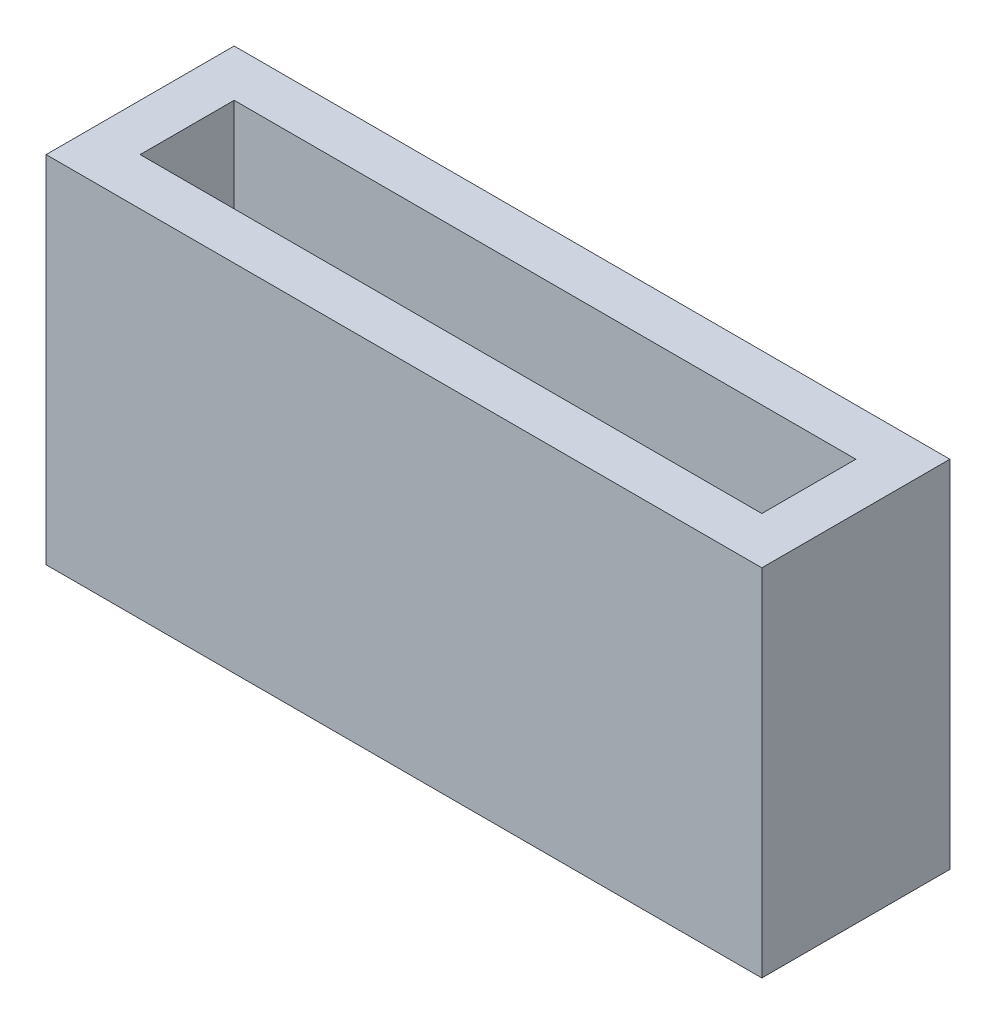
SolidWorks part; units mm, degrees
ref_plane "Front Plane" through (0, 0, 0) normal (0, 0, 1) x (1, 0, 0)
ref_plane "Top Plane" through (0, 0, 0) normal (0, 1, 0) x (1, 0, 0)
ref_plane "Right Plane" through (0, 0, 0) normal (1, 0, 0) x (0, 0, -1)
sketch "Sketch1" plane through (0, 0, 0) normal (0, 1, 0) x (1, 0, 0)
  line L1 (-55.1703, -19.7188) -> (-20.9203, -19.7188)
  line L2 (-55.1703, -19.7188) -> (-55.1703, -28.7188)
  line L3 (-55.1703, -28.7188) -> (-20.9203, -28.7188)
  line L4 (-20.9203, -19.7188) -> (-20.9203, -28.7188)
extrude "Boss-Extrude1" add sketch "Sketch1" along normal blind 17
sketch "Sketch2" plane through (0, 17, 0) normal (0, 1, 0) x (1, 0, 0)
  line L8 (-52.9203, -21.9688) -> (-52.9203, -26.4688)
  line L9 (-52.9203, -26.4688) -> (-23.1703, -26.4688)
  line L10 (-23.1703, -26.4688) -> (-23.1703, -21.9688)
  line L11 (-23.1703, -21.9688) -> (-52.9203, -21.9688)
  line L12 (-52.9203, -21.9688) -> (-52.9203, -26.4688)
  line L13 (-52.9203, -26.4688) -> (-23.1703, -26.4688)
  line L14 (-23.1703, -26.4688) -> (-23.1703, -21.9688)
  line L15 (-23.1703, -21.9688) -> (-52.9203, -21.9688)
  dimension "D1" = 2.25
extrude "Cut-Extrude1" cut sketch "Sketch2" against normal blind 15
